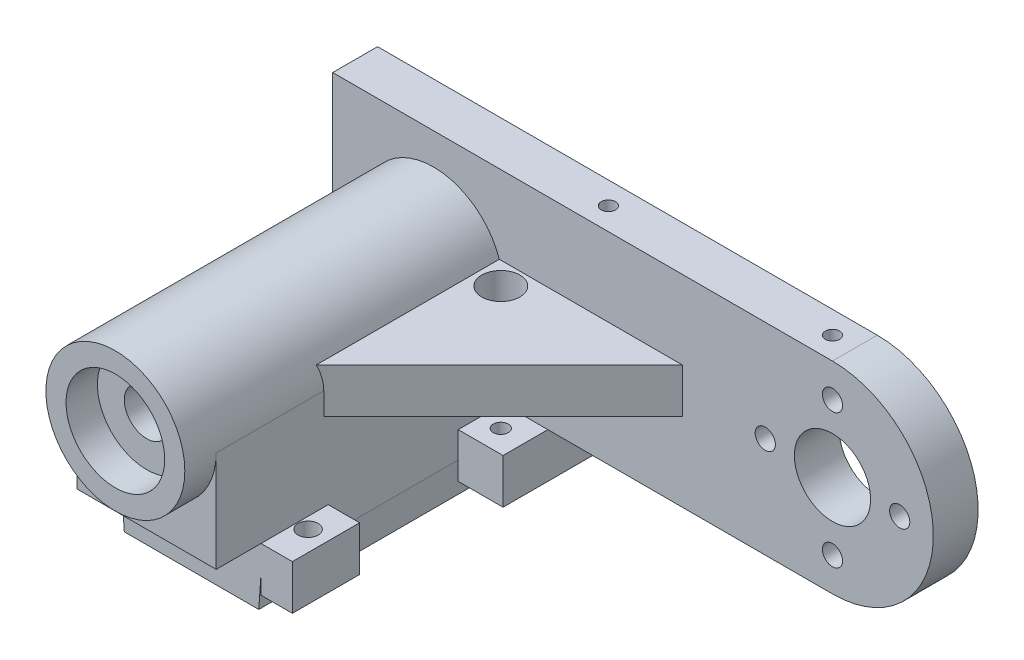
SolidWorks part; units mm, degrees
ref_plane "Front Plane" through (0, 0, 0) normal (0, 0, 1) x (1, 0, 0)
ref_plane "Top Plane" through (0, 0, 0) normal (0, 1, 0) x (1, 0, 0)
ref_plane "Right Plane" through (0, 0, 0) normal (1, 0, 0) x (0, 0, -1)
sketch "Sketch1" plane through (0, 0, 0) normal (0, 1, 0) x (1, 0, 0)
  line L0 (-23, 32) -> (-23, 22)
  line L1 (0, 0) -> (-26, 0)
  line L2 (0, 0) -> (0, 53)
  line L3 (0, 53) -> (-26, 53)
  line L4 (-26, 0) -> (-26, 53)
  line L5 (-23, 48) -> (-3, 48)
  line L6 (-23, 48) -> (-23, 38)
  line L7 (-23, 38) -> (-3, 38)
  line L8 (-3, 48) -> (-3, 38)
  line L9 (-23, 32) -> (-3, 32)
  line L10 (-3, 32) -> (-3, 22)
  line L11 (-23, 22) -> (-3, 22)
  line L12 (-23, 16) -> (-23, 6)
  line L13 (-23, 16) -> (-3, 16)
  line L14 (-3, 16) -> (-3, 6)
  line L15 (-23, 6) -> (-3, 6)
  point P9 (-13, 48)
  point P10 (-13, 53)
  dimension "D1" = 26
  dimension "D2" = 53
  dimension "D3" = 20
  dimension "D4" = 10
  dimension "D5" = 5
  dimension "D6" = 3
extrude "Boss-Extrude1" add sketch "Sketch1" along normal blind 5
sketch "Sketch2" plane through (0, 5, 0) normal (0, 1, 0) x (1, 0, 0)
  line L17 (-26, 53) -> (0, 53)
  line L18 (-26, 53) -> (-26, 0)
  line L19 (-26, 0) -> (0, 0)
  line L20 (0, 53) -> (0, 0)
  line L21 (-28.5, 56) -> (2.5, 56)
  line L22 (-28.5, 56) -> (-28.5, -3)
  line L23 (-28.5, -3) -> (2.5, -3)
  line L24 (2.5, 56) -> (2.5, -3)
  dimension "D1" = 3
  dimension "D2" = 2.5
  dimension "D3" = 2.5
  dimension "D4" = 3
extrude "Boss-Extrude2" add sketch "Sketch2" against normal blind 10
sketch "Sketch3" plane through (0, 5, 0) normal (0, 1, 0) x (1, 0, 0)
  line L1 (-28.5, 56) -> (2.5, 56)
  line L2 (-28.5, 56) -> (-28.5, -3)
  line L3 (-28.5, -3) -> (2.5, -3)
  line L4 (2.5, 56) -> (2.5, -3)
extrude "Boss-Extrude3" add sketch "Sketch3" along normal blind 3
sketch "Sketch4" plane through (0, 8, 0) normal (0, 1, 0) x (1, 0, 0)
  line L1 (-5, 56) -> (-11, 56)
  line L2 (-5, 56) -> (-5, 10)
  line L3 (-5, 10) -> (-11, 10)
  line L4 (-11, 56) -> (-11, 10)
  line L6 (-3, 38) -> (-3, 48) construction
  line L8 (-28.5, -3) -> (2.5, -3) construction
  dimension "D1" = 6
  dimension "D2" = 2
  dimension "D3" = 46
  dimension "D4" = 13
extrude "Boss-Extrude4" [suppressed] add sketch "Sketch4" along normal blind 55
sketch "Sketch5" [suppressed] plane through (-5, 0, 0) normal (1, 0, 0) x (0, 0, -1)
  line L0 (10, 8) -> (56, 8) construction
  line L1 (56, 63) -> (56, 8) construction
  line L2 (19, 48) -> (50, 17) construction
  line L3 (50, 48) -> (19, 17) construction
  circle A0 centre (50, 17) radius 1.75
  circle A1 centre (19, 17) radius 1.75
  circle A2 centre (19, 48) radius 1.75
  circle A3 centre (50, 48) radius 1.75
  circle A4 centre (34.5, 32.5) radius 13.5
  dimension "D2" = 6
  dimension "D3" = 3.5
  dimension "D6" = 27
  dimension "D1" = 9
  dimension "D4" = 2
  dimension "D5" = 2
extrude "Cut-Extrude1" [suppressed] cut sketch "Sketch5" against normal through all
chamfer "Chamfer1" distance 0.5 angle 86 2 edges at (2.5, -5, -26.5) (-28.5, -5, -26.5)
sketch "Sketch6" [suppressed] plane through (-5, 0, 0) normal (1, 0, 0) x (0, 0, -1)
  line L0 (10, 63) -> (10, 8) construction
  line L1 (56, 63) -> (10, 63)
  line L2 (56, 63) -> (56, 56)
  line L3 (56, 56) -> (10, 56)
  line L4 (10, 63) -> (10, 56)
  dimension "D1" = 7
extrude "Boss-Extrude5" [suppressed] add sketch "Sketch6" along normal blind 14
sketch "Sketch7" [suppressed] plane through (0, 63, 0) normal (0, 1, 0) x (1, 0, 0)
  line L0 (-11, 56) -> (-11, 10) construction
  line L1 (-8.5, 39.5) -> (-3.5, 39.5)
  line L2 (-8.5, 39.5) -> (-8.5, 34.5)
  line L3 (-8.5, 34.5) -> (-3.5, 34.5)
  line L4 (-3.5, 39.5) -> (-3.5, 34.5)
  line L5 (1.5, 39.5) -> (6.5, 39.5)
  line L6 (1.5, 39.5) -> (1.5, 34.5)
  line L7 (1.5, 34.5) -> (6.5, 34.5)
  line L8 (6.5, 39.5) -> (6.5, 34.5)
  line L9 (-8.5, 16.5) -> (-3.5, 16.5)
  line L10 (-8.5, 16.5) -> (-8.5, 11.5)
  line L11 (-8.5, 11.5) -> (-3.5, 11.5)
  line L12 (-3.5, 16.5) -> (-3.5, 11.5)
  line L13 (1.5, 16.5) -> (6.5, 16.5)
  line L14 (1.5, 16.5) -> (1.5, 11.5)
  line L15 (1.5, 11.5) -> (6.5, 11.5)
  line L16 (6.5, 16.5) -> (6.5, 11.5)
  line L17 (-11, 10) -> (9, 10) construction
  point P18 (-6, 16.5)
  point P19 (-6, 39.5)
  point P20 (4, 39.5)
  point P21 (4, 16.5)
  point P22 (-3.5, 37)
  point P23 (1.5, 37)
  point P24 (-3.5, 14)
  point P25 (1.5, 14)
  dimension "D1" = 5
  dimension "D2" = 5
  dimension "D3" = 2.5
  dimension "D4" = 1.5
  dimension "D5" = 23
extrude "Cut-Extrude2" [suppressed] cut sketch "Sketch7" against normal blind 5
sketch "Sketch8" [suppressed] plane through (0, 0, -56) normal (0, 0, -1) x (-1, 0, 0)
  line L0 (-9, 56) -> (-9, 63) construction
  line L1 (-9, 8) -> (5.6893, 8)
  line L2 (-9, 8) -> (-9, 1)
  line L3 (-9, 1) -> (5.6893, 1)
  line L4 (5.6893, 8) -> (5.6893, 1)
  line L5 (-2.5, 8) -> (5, 8) construction
extrude "Boss-Extrude6" [suppressed] add sketch "Sketch8" against normal blind 7.5
sketch "Sketch9" [suppressed] plane through (0, 0, -56) normal (0, 0, -1) x (-1, 0, 0)
  line L0 (-9, 56) -> (-9, 63) construction
  line L1 (-9, 8) -> (-9, 1) construction
  line L2 (11, 63) -> (11, 8) construction
  line L3 (5, 56) -> (5, 8) construction
  line L4 (-9, 8) -> (5, 8) construction
  line L6 (-9, 56) -> (5, 56) construction
  circle A0 centre (-5.5, 59.5) radius 1.75
  circle A1 centre (-5.5, 4.5) radius 1.75
  circle A2 centre (8, 54) radius 1.75
  circle A3 centre (8, 10) radius 1.75
  circle A4 centre (8, 32) radius 1.75
  point P5 (-9, 59.5)
  point P9 (-9, 4.5)
  dimension "D1" = 3.5
  dimension "D2" = 3.5
  dimension "D3" = 3.5
  dimension "D4" = 3.5
  dimension "D5" = 3
  dimension "D6" = 3
  dimension "D7" = 3
  dimension "D8" = 2
  dimension "D9" = 2
  dimension "D10" = 22
  dimension "D11" = 22
extrude "Cut-Extrude3" [suppressed] cut sketch "Sketch9" against normal blind 4
sketch "Sketch10" plane through (0, 8, 0) normal (0, 1, 0) x (1, 0, 0)
  line L0 (-13, -3) -> (-13, 56) construction
  line L1 (2.5, -3) -> (9.5, -3)
  line L2 (2.5, -3) -> (2.5, 12)
  line L3 (2.5, 12) -> (9.5, 12)
  line L4 (9.5, -3) -> (9.5, 12)
  line L9 (-28.5, -3) -> (2.5, -3) construction
  line L10 (2.5, 56) -> (-28.5, 56) construction
  line L11 (-28.5, 12) -> (-35.5, 12)
  line L12 (-35.5, -3) -> (-35.5, 12)
  line L13 (-28.5, -3) -> (-35.5, -3)
  line L14 (-28.5, -3) -> (-28.5, 12)
  circle A0 centre (5, 5) radius 2.25
  circle A1 centre (-31, 5) radius 2.25
  dimension "D6" = 4.5
  dimension "D3" = 4.5
  dimension "D1" = 15
  dimension "D2" = 7
  dimension "D5" = 8
extrude "Boss-Extrude7" add sketch "Sketch10" against normal blind 10
sketch "Sketch11" plane through (0, 8, 0) normal (0, 1, 0) x (1, 0, 0)
  line L1 (-35.5, 12) -> (-28.5, 12)
  line L2 (-35.5, 12) -> (-35.5, 9)
  line L3 (-35.5, 9) -> (-28.5, 9)
  line L4 (-28.5, 12) -> (-28.5, 9)
  dimension "D1" = 3
extrude "Cut-Extrude4" cut sketch "Sketch11" against normal blind 10
chamfer "Chamfer2" distance 2 angle 64 1 edges at (-35.5, 3, -9)
sketch "Sketch12" plane through (0, 8, 0) normal (0, 1, 0) x (1, 0, 0)
  line L0 (2.5, 12) -> (2.5, 56) construction
  line L1 (2.5, 56) -> (-28.5, 56) construction
  line L2 (-13, 56) -> (-13, 17.5206) construction
  line L3 (2.5, 56) -> (12.5, 56)
  line L4 (2.5, 56) -> (2.5, 41)
  line L5 (2.5, 41) -> (12.5, 41)
  line L6 (12.5, 56) -> (12.5, 41)
  line L7 (-28.5, 41) -> (-38.5, 41)
  line L8 (-38.5, 56) -> (-38.5, 41)
  line L9 (-28.5, 56) -> (-38.5, 56)
  line L10 (-28.5, 56) -> (-28.5, 41)
  circle A0 centre (7, 46) radius 1.6764
  circle A1 centre (-33, 46) radius 1.6764
  dimension "D1" = 4.5
  dimension "D2" = 10
  dimension "D3" = 15
  dimension "D4" = 10
extrude "Boss-Extrude8" add sketch "Sketch12" against normal up to surface (10 mm away) up to face at (5, -2, -2.75)
sketch "Sketch15" plane through (0, 0, 0) normal (0, 0, 1) x (1, 0, 0)
  line L0 (-13, 53) -> (76, 53)
  line L1 (76, 8) -> (-13, 8)
  line L8 (12.5, 8) -> (-38.5, 8) construction
  line L9 (2, -5) -> (-28, -5) construction
  line L11 (-13, 53) -> (-35.5, 53)
  line L13 (-13, 8) -> (-35.5, 8)
  line L14 (-35.5, 53) -> (-35.5, 8)
  arc A0 (76, 8) -> (76, 53) centre (76, 30.5) ccw
  circle A1 centre (76, 30.5) radius 8.5
  circle A3 centre (76, 45.5) radius 2.25
  circle A4 centre (76, 15.5) radius 2.25
  circle A5 centre (91, 30.5) radius 2.25
  circle A6 centre (61, 30.5) radius 2.25
  circle A7 centre (-13, 30.5) radius 11
  point P21 (-13, -5)
  dimension "D1" = 45
  dimension "D2" = 17
  dimension "D3" = 22
  dimension "D4" = 4.5
  dimension "D7" = 15
  dimension "D8" = 15
  dimension "D9" = 15
  dimension "D5" = 89
  dimension "D6" = 15
  dimension "D10" = 0
  dimension "D11" = 0
extrude "Boss-Extrude9" add sketch "Sketch15" along normal blind 5 and the other way blind 5 from surface at -56 starting at face at (-13, 0.2301, -56)
sketch "Sketch16" plane through (0, 0, -51) normal (0, 0, 1) x (1, 0, 0)
  line L4 (-35.5, 53) -> (-35.5, 8)
  line L5 (-35.5, 8) -> (12.5, 8)
  line L6 (12.5, 8) -> (76, 8)
  line L7 (76, 53) -> (-35.5, 53)
  line L8 (-35.5, 53) -> (-35.5, 8)
  line L9 (-35.5, 8) -> (12.5, 8)
  line L10 (12.5, 8) -> (76, 8)
  line L11 (76, 53) -> (-35.5, 53)
  circle A0 centre (76, 45.5) radius 2.25 construction
  arc A1 (76, 8) -> (76, 53) centre (76, 30.5) ccw
  arc A2 (76, 8) -> (76, 53) centre (76, 30.5) ccw
  circle A3 centre (91, 30.5) radius 2.25 construction
  circle A4 centre (76, 15.5) radius 2.25 construction
  circle A5 centre (76, 30.5) radius 8.5 construction
  circle A6 centre (61, 30.5) radius 2.25 construction
  circle A7 centre (76, 45.5) radius 2.25
  circle A8 centre (91, 30.5) radius 2.25
  circle A9 centre (76, 15.5) radius 2.25
  circle A10 centre (76, 30.5) radius 8.5
  circle A11 centre (61, 30.5) radius 2.25
  circle A12 centre (-13, 30.5) radius 5
  dimension "D2" = 10
  dimension "D1" = 0
extrude "Boss-Extrude10" add sketch "Sketch16" against normal blind 2
sketch "Sketch17" plane through (0, 0, -51) normal (0, 0, 1) x (1, 0, 0)
  line L0 (12.5, 8) -> (-35.5, 8) construction
  line L2 (-28.5, 30.5) -> (-28.5, 8)
  line L3 (-28.5, 8) -> (2.5, 8)
  line L4 (2.5, 30.5) -> (2.5, 8)
  circle A0 centre (-13, 30.5) radius 5
  arc A1 (2.5, 30.5) -> (-28.5, 30.5) centre (-13, 30.5) ccw
  dimension "D1" = 31
extrude "Boss-Extrude11" add sketch "Sketch17" along normal blind 64
ref_plane "Plane1" through (0, 30.5, 0) normal (0, 1, 0) x (0, 0, -1)
sketch "Sketch20" plane through (0, 30.5, 0) normal (0, 1, 0) x (0, 0, -1)
  line L1 (-3, -2.5) -> (12, -2.5) construction
  line L3 (51, 35.5) -> (51, -76) construction
  line L4 (51, -42.5) -> (11, -2.5)
rib "Rib2" sketch "Sketch20" sketch "Sketch20" thickness 10 extrusion direction parallel to sketch draft on no parameters "D1"=10
sketch "Sketch21" plane through (0, 0, -56) normal (0, 0, -1) x (-1, 0, 0)
  line L11 (-2, -5) -> (28, -5)
  line L12 (28, -5) -> (28.5, 2.1503)
  line L13 (28.5, 2.1503) -> (28.5, -2)
  line L14 (28.5, -2) -> (38.5, -2)
  line L15 (38.5, -2) -> (38.5, 8)
  line L16 (38.5, 8) -> (35.5, 8)
  line L17 (35.5, 8) -> (-12.5, 8)
  line L18 (-12.5, 8) -> (-12.5, -2)
  line L19 (-12.5, -2) -> (-2.5, -2)
  line L20 (-2.5, -2) -> (-2.5, 2.1503)
  line L21 (-2.5, 2.1503) -> (-2, -5)
  line L22 (-2, -5) -> (28, -5)
  line L23 (28, -5) -> (28.5, 2.1503)
  line L24 (28.5, 2.1503) -> (28.5, -2)
  line L25 (28.5, -2) -> (38.5, -2)
  line L26 (38.5, -2) -> (38.5, 8)
  line L27 (38.5, 8) -> (35.5, 8)
  line L28 (35.5, 8) -> (-12.5, 8)
  line L29 (-12.5, 8) -> (-12.5, -2)
  line L30 (-12.5, -2) -> (-2.5, -2)
  line L31 (-2.5, -2) -> (-2.5, 2.1503)
  line L32 (-2.5, 2.1503) -> (-2, -5)
  dimension "D1" = 0
extrude "Boss-Extrude12" add sketch "Sketch21" along normal up to surface (5 mm away) up to face at (-24, 30.5, -61)
sketch "Sketch22" plane through (0, 0, 13) normal (0, 0, 1) x (1, 0, 0)
  circle A0 centre (-13, 30.5) radius 11
  circle A1 centre (-13, 30.5) radius 15.5
  dimension "D1" = 22
extrude "Boss-Extrude13" add sketch "Sketch22" along normal blind 7
sketch "Sketch23" plane through (0, 8, 0) normal (0, 1, 0) x (1, 0, 0)
  circle A0 centre (7, 46) radius 4.25
  dimension "D1" = 8.5
extrude "Cut-Extrude5" cut sketch "Sketch23" along normal blind 29
sketch "Sketch24" plane through (-35.5, 0, 0) normal (-1, 0, 0) x (0, 0, 1)
  line L0 (-61, 53) -> (-51, 53) construction
  circle A0 centre (-56, 28) radius 1.6
  circle A1 centre (-56, 43) radius 1.6
  point P4 (0, 0)
  point P7 (-56, 53)
  dimension "D2" = 3.2
  dimension "D3" = 15
  dimension "D1" = 10
extrude "Cut-Extrude6" cut sketch "Sketch24" against normal blind 8
sketch "Sketch25" plane through (0, 53, 0) normal (0, 1, 0) x (1, 0, 0)
  line L0 (76, 61) -> (76, 51) construction
  circle A0 centre (71, 56) radius 1.6
  circle A1 centre (21, 56) radius 1.6
  dimension "D3" = 3.2
  dimension "D1" = 50
  dimension "D2" = 5
extrude "Cut-Extrude7" cut sketch "Sketch25" against normal blind 8
